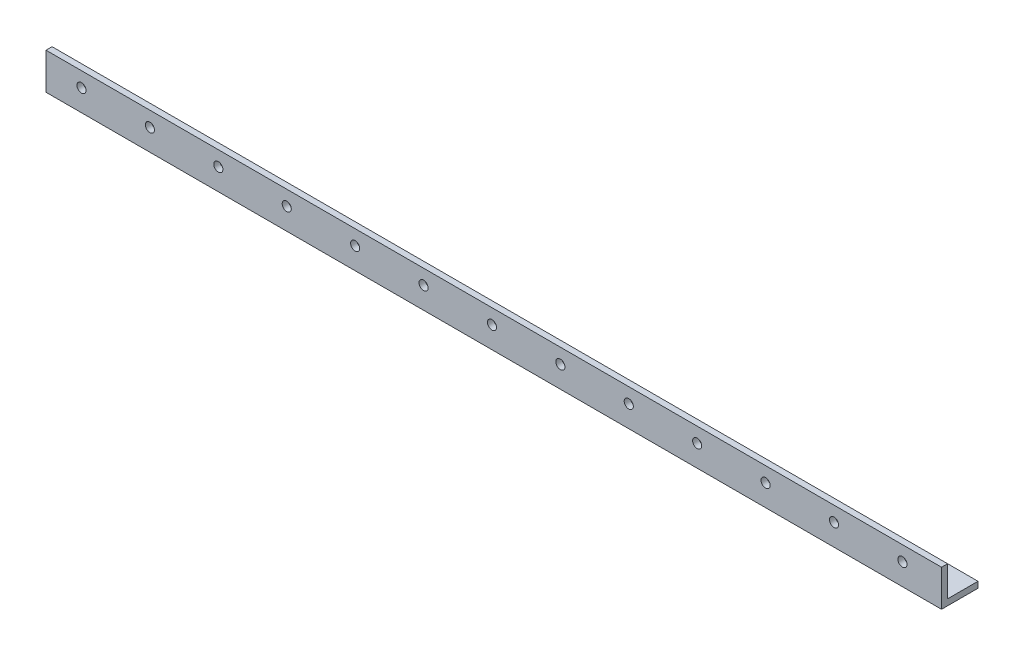
SolidWorks part; units mm, degrees
ref_plane "Front Plane" through (0, 0, 0) normal (0, 0, 1) x (1, 0, 0)
ref_plane "Top Plane" through (0, 0, 0) normal (0, 1, 0) x (1, 0, 0)
ref_plane "Right Plane" through (0, 0, 0) normal (1, 0, 0) x (0, 0, -1)
sketch "Sketch1" plane through (0, 0, 0) normal (1, 0, 0) x (0, 0, -1)
  line L0 (0, 0) -> (0, 19.05)
  line L1 (0, 19.05) -> (3.175, 19.05)
  line L2 (3.175, 19.05) -> (3.175, 3.175)
  line L3 (3.175, 3.175) -> (19.05, 3.175)
  line L4 (19.05, 3.175) -> (19.05, 0)
  line L5 (19.05, 0) -> (0, 0)
extrude "Boss-Extrude1" add sketch "Sketch1" against normal blind 468
sketch "Sketch2" plane through (0, 0, 0) normal (0, 0, 1) x (1, 0, 0)
  circle A0 centre (-449.45, 11.2735) radius 2.3813
  circle A1 centre (-413.7, 11.2735) radius 2.3813
  circle A2 centre (-377.95, 11.2735) radius 2.3813
  circle A3 centre (-342.2, 11.2735) radius 2.3813
  circle A4 centre (-306.45, 11.2735) radius 2.3813
  circle A5 centre (-270.7, 11.2735) radius 2.3813
  circle A6 centre (-234.95, 11.2735) radius 2.3813
  circle A7 centre (-199.2, 11.2735) radius 2.3813
  circle A8 centre (-163.45, 11.2735) radius 2.3813
  circle A9 centre (-127.7, 11.2735) radius 2.3813
  circle A10 centre (-91.95, 11.2735) radius 2.3813
  circle A11 centre (-56.2, 11.2735) radius 2.3812
  circle A12 centre (-20.45, 11.2735) radius 2.3813
extrude "Cut-Extrude1" cut sketch "Sketch2" against normal blind 3.175
